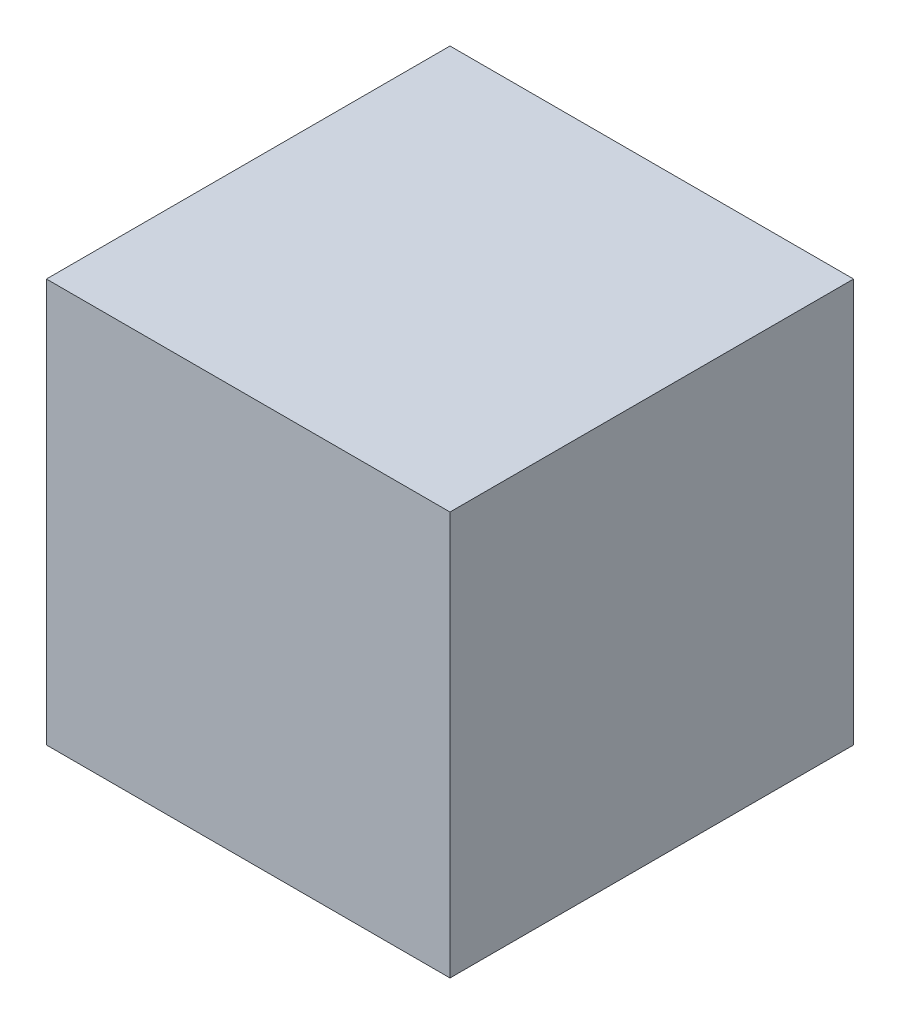
SolidWorks part; units mm, degrees
ref_plane "Front" through (0, 0, 0) normal (0, 0, 1) x (1, 0, 0)
ref_plane "Top" through (0, 0, 0) normal (0, 1, 0) x (1, 0, 0)
ref_plane "Right" through (0, 0, 0) normal (1, 0, 0) x (0, 0, -1)
sketch "Sketch1" plane through (0, 0, 0) normal (0, 1, 0) x (1, 0, 0)
  line L1 (-25.4, -25.4) -> (25.4, -25.4)
  line L2 (-25.4, -25.4) -> (-25.4, 25.4)
  line L3 (-25.4, 25.4) -> (25.4, 25.4)
  line L4 (25.4, -25.4) -> (25.4, 25.4)
  line L5 (-25.4, -25.4) -> (25.4, 25.4) construction
  line L6 (-25.4, 25.4) -> (25.4, -25.4) construction
  point P0 (0, 0)
  dimension "D1" = 50.8
extrude "Boss-Extrude1" add sketch "Sketch1" along normal mid plane 50.8
equation "\"length\"=50.8"
equation "\"D1@Sketch1\"=\"length\""
equation "\"D1@Boss-Extrude1\"=\"length\""
